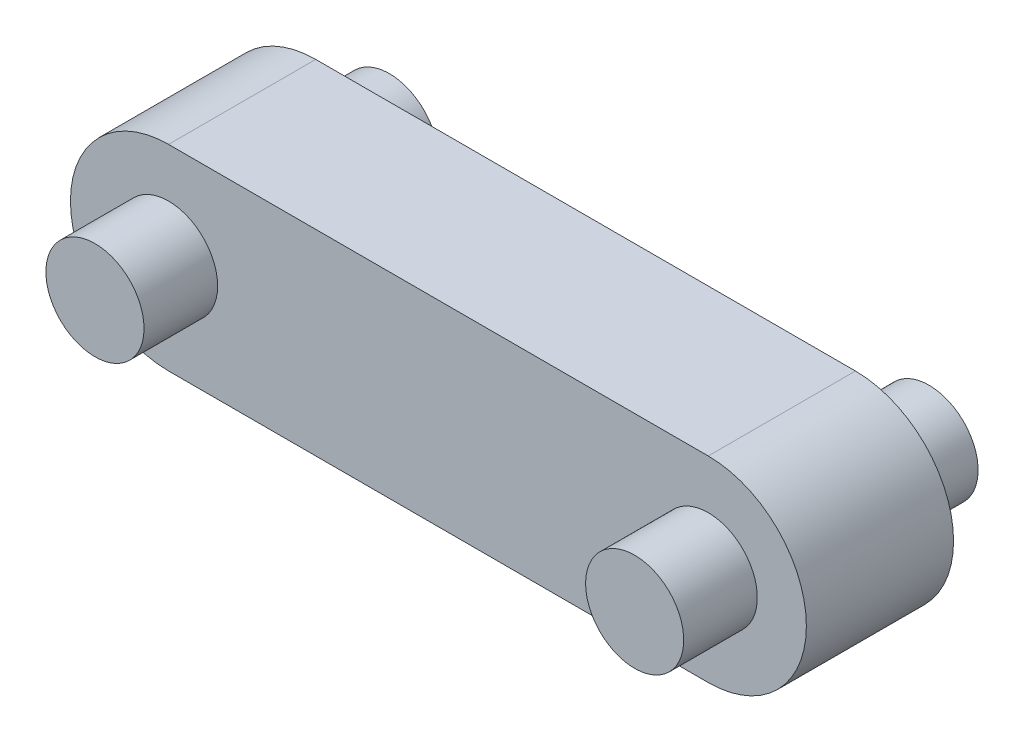
SolidWorks part; units mm, degrees
ref_plane "Front Plane" through (0, 0, 0) normal (0, 0, 1) x (1, 0, 0)
ref_plane "Top Plane" through (0, 0, 0) normal (0, 1, 0) x (1, 0, 0)
ref_plane "Right Plane" through (0, 0, 0) normal (1, 0, 0) x (0, 0, -1)
sketch "Sketch1" plane through (0, 0, 0) normal (0, 0, 1) x (1, 0, 0)
  circle A0 centre (0, 0) radius 10
  dimension "D1" = 20
extrude "Boss-Extrude1" add sketch "Sketch1" along normal mid plane 60
sketch "Sketch2" plane through (0, 0, 0) normal (0, 0, 1) x (1, 0, 0)
  line L0 (0, 20) -> (55, 20)
  line L1 (55, 20) -> (55, -20)
  line L2 (55, -20) -> (0, -20)
  arc A0 (0, 20) -> (0, -20) centre (0, 0) ccw
  dimension "D1" = 40
  dimension "D2" = 55
extrude "Boss-Extrude2" add sketch "Sketch2" along normal mid plane 30
mirror "Mirror1" about plane through (55, 20, 15) normal (-1, 0, 0) of "Boss-Extrude2", "Boss-Extrude1"
